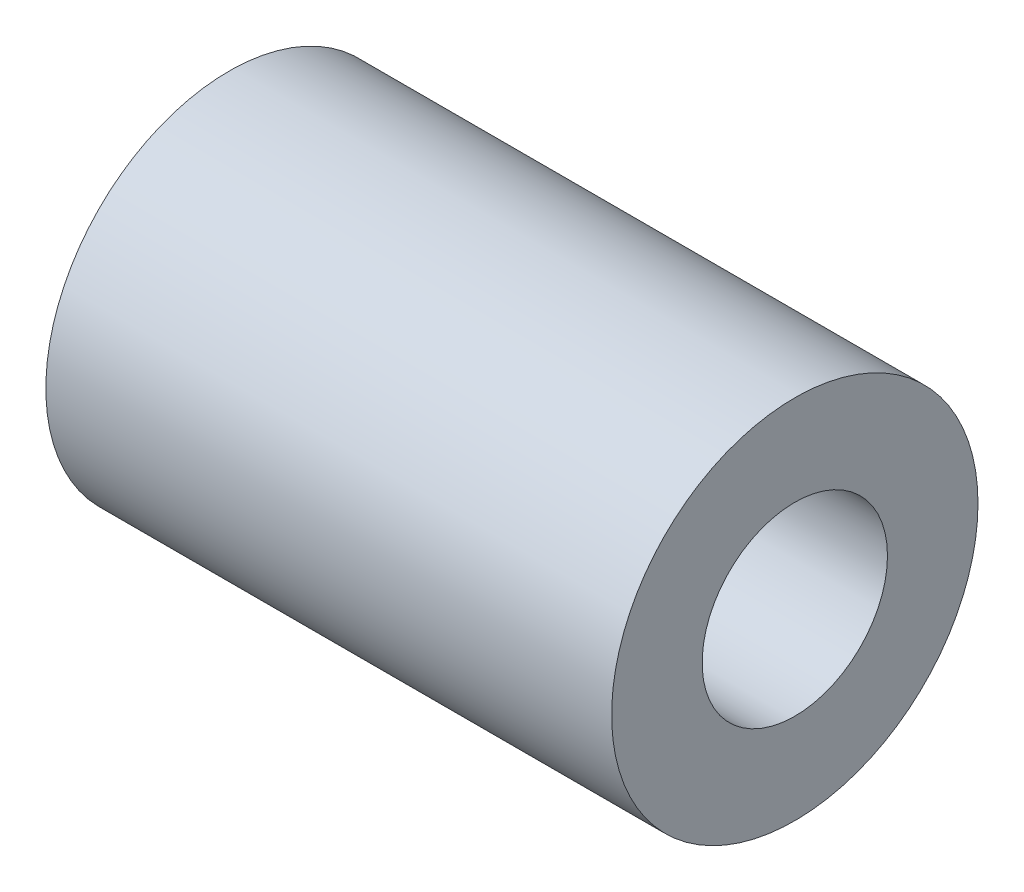
SolidWorks part; units mm, degrees
ref_plane "Front Plane" through (0, 0, 0) normal (0, 0, 1) x (1, 0, 0)
ref_plane "Top Plane" through (0, 0, 0) normal (0, 1, 0) x (1, 0, 0)
ref_plane "Right Plane" through (0, 0, 0) normal (1, 0, 0) x (0, 0, -1)
sketch "Sketch1" plane through (0, 0, 0) normal (1, 0, 0) x (0, 0, -1)
  circle A0 centre (0, 0) radius 2.6
  circle A1 centre (0, 0) radius 5.14
  dimension "D1" = 5.2
  dimension "D2" = 2.54
extrude "Boss-Extrude1" add sketch "Sketch1" along normal blind 15.875
